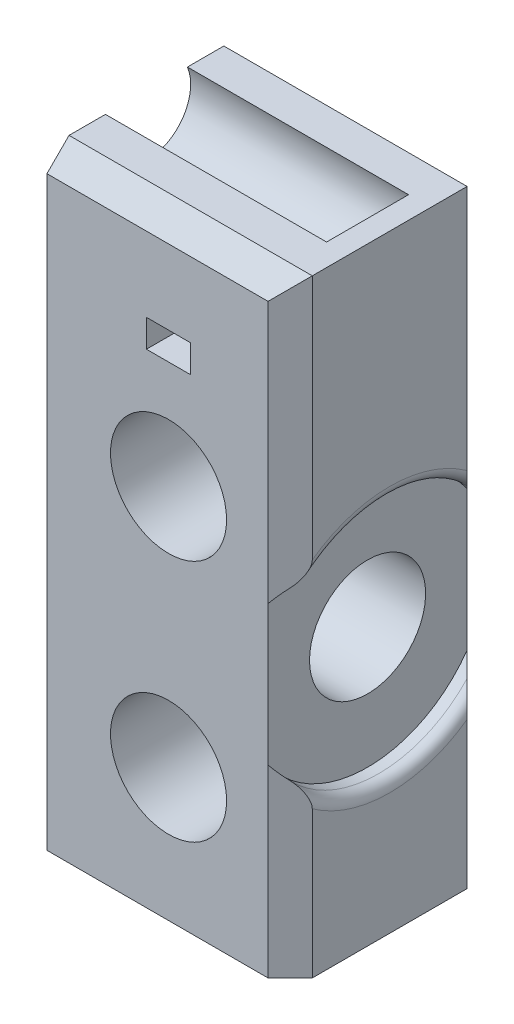
SolidWorks part; units mm, degrees
material "ABS generico"
ref_plane "Piano frontale" through (0, 0, 0) normal (0, 0, 1) x (1, 0, 0)
ref_plane "Piano superiore" through (0, 0, 0) normal (0, 1, 0) x (1, 0, 0)
ref_plane "Piano destro" through (0, 0, 0) normal (1, 0, 0) x (0, 0, -1)
sketch "Sketch1" plane through (0, 0, 0) normal (0, 0, 1) x (1, 0, 0)
  line L0 (0, 0) -> (0, 55)
  line L1 (0, 55) -> (22, 55)
  line L2 (22, 55) -> (22, 0)
  line L3 (22, 0) -> (0, 0)
  line L4 (11, 55) -> (11, 0) construction
  line L6 (13, 43.75) -> (9, 43.75)
  line L7 (13, 43.75) -> (13, 46.25)
  line L8 (13, 46.25) -> (9, 46.25)
  line L9 (9, 43.75) -> (9, 46.25)
  line L10 (13, 43.75) -> (9, 46.25) construction
  line L11 (13, 46.25) -> (9, 43.75) construction
  circle A0 centre (11, 12) radius 5.25
  circle A1 centre (11, 34) radius 5.25
  point P11 (11, 45)
  dimension "D5" = 10.5
  dimension "D1" = 22
  dimension "D2" = 55
  dimension "D3" = 12
  dimension "D4" = 34
  dimension "D6" = 10
  dimension "D7" = 4
  dimension "D8" = 2.5
extrude "Boss-Extrude1" add sketch "Sketch1" against normal blind 18
sketch "Sketch2" plane through (0, 0, 0) normal (-1, 0, 0) x (0, 0, 1)
  line L0 (-9, 0) -> (-9, 55) construction
  line L1 (-18, 0) -> (0, 0) construction
  line L2 (-18, 55) -> (0, 55) construction
  circle A0 centre (-9, 23) radius 5.25
  dimension "D2" = 10.5
  dimension "D1" = 23
extrude "Cut-Extrude1" cut sketch "Sketch2" against normal through all
sketch "Sketch3" plane through (0, 0, 0) normal (1, 0, 0) x (0, 0, -1)
  line L0 (9, 55) -> (9, 62.8182) construction
  line L2 (18, 55) -> (0, 55) construction
  circle A0 centre (9, 53.5) radius 4
  dimension "D1" = 8
  dimension "D2" = 1.5
extrude "Cut-Extrude2" cut sketch "Sketch3" along normal blind 20
chamfer "Chamfer1" distance 2 angle 45 2 edges at (22, 27.5, 0) (22, 27.5, -18)
sketch "Sketch4" plane through (22, 0, 0) normal (1, 0, 0) x (0, 0, -1)
  circle A0 centre (9, 23) radius 11
  dimension "D1" = 22
extrude "Cut-Extrude3" cut sketch "Sketch4" against normal blind 2
fillet "Fillet1" radius 1 2 edges at (22, 34, -9) (22, 12, -9)
chamfer "Chamfer2" distance 2 angle 45 2 edges at (10, 55, 0) (10, 55, -18)
